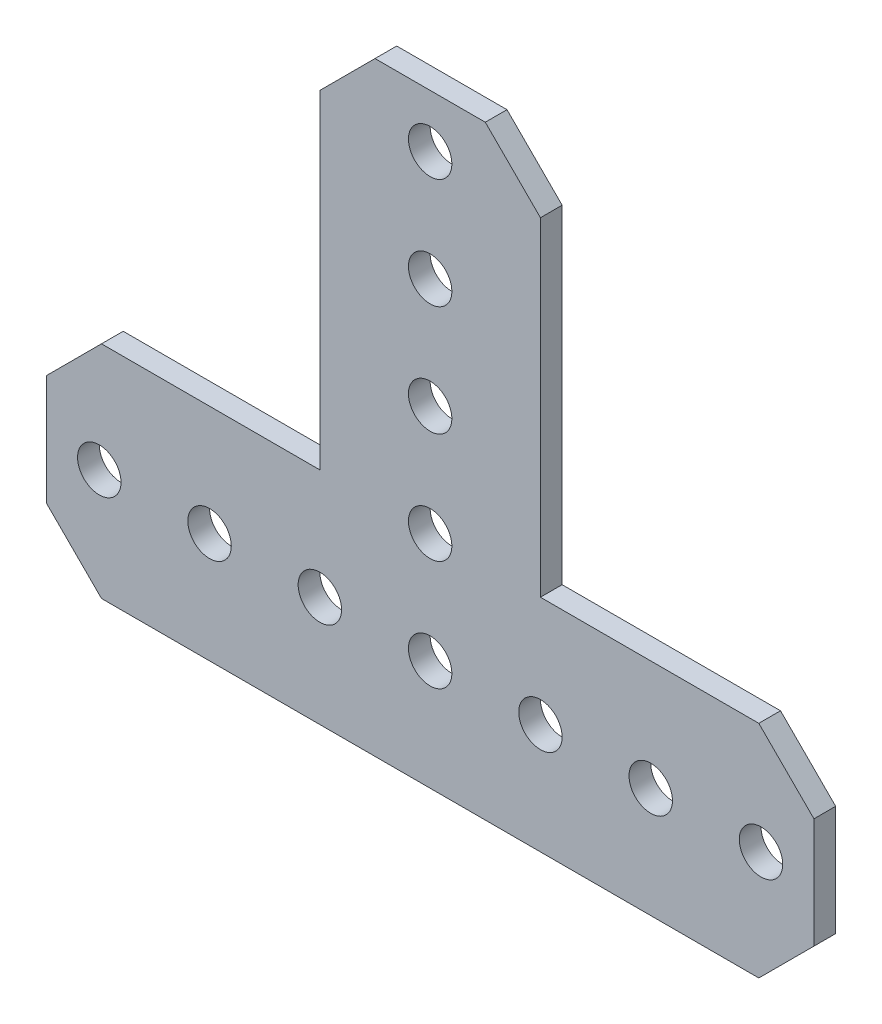
SolidWorks part; units mm, degrees
material "5052-H32"
ref_plane "Front Plane" through (0, 0, 0) normal (0, 0, 1) x (1, 0, 0)
ref_plane "Top Plane" through (0, 0, 0) normal (0, 1, 0) x (1, 0, 0)
ref_plane "Right Plane" through (0, 0, 0) normal (1, 0, 0) x (0, 0, -1)
ref_plane "Plane1" through (0, 0, -1.25) normal (0, 0, -1) x (-1, 0, 0)
sketch "Sketch1" plane through (0, 0, -1.25) normal (0, 0, -1) x (-1, 0, 0)
  line L0 (12.7, 12.7) -> (12.7, 50.546)
  line L1 (12.7, 50.546) -> (6.35, 56.896)
  line L2 (6.35, 56.896) -> (-6.35, 56.896)
  line L3 (-6.35, 56.896) -> (-12.7, 50.546)
  line L4 (-12.7, 50.546) -> (-12.7, 12.7)
  line L5 (-12.7, 12.7) -> (-37.846, 12.7)
  line L6 (-37.846, 12.7) -> (-44.196, 6.35)
  line L7 (-44.196, 6.35) -> (-44.196, -6.35)
  line L8 (-44.196, -6.35) -> (-37.846, -12.7)
  line L9 (-37.846, -12.7) -> (37.846, -12.7)
  line L10 (37.846, -12.7) -> (44.196, -6.35)
  line L11 (44.196, -6.35) -> (44.196, 6.35)
  line L12 (44.196, 6.35) -> (37.846, 12.7)
  line L13 (37.846, 12.7) -> (12.7, 12.7)
  circle A0 centre (0, 50.8) radius 2.5
  circle A1 centre (0, 38.1) radius 2.5
  circle A2 centre (-38.1, 0) radius 2.5
  circle A3 centre (-25.4, 0) radius 2.5
  circle A4 centre (-12.7, 0) radius 2.5
  circle A5 centre (0, 0) radius 2.5
  circle A6 centre (12.7, 0) radius 2.5
  circle A7 centre (38.1, 0) radius 2.5
  circle A8 centre (25.4, 0) radius 2.5
  circle A9 centre (0, 12.7) radius 2.5
  circle A10 centre (0, 25.4) radius 2.5
  point P36 (0, 0)
  dimension "D1" = 5
  dimension "D2" = 5
  dimension "D3" = 5
  dimension "D4" = 5
  dimension "D5" = 5
  dimension "D6" = 5
  dimension "D7" = 5
  dimension "D8" = 5
  dimension "D9" = 5
  dimension "D10" = 5
  dimension "D11" = 5
  dimension "D12" = 6.096
  dimension "D13" = 6.35
  dimension "D14" = 18.796
  dimension "D15" = 31.496
  dimension "D16" = 37.846
  dimension "D17" = 44.196
  dimension "D18" = 50.546
  dimension "D19" = 56.896
  dimension "D20" = 69.596
  dimension "D21" = 82.042
  dimension "D22" = 82.296
  dimension "D23" = 88.392
  dimension "D24" = 6.096
  dimension "D25" = 6.35
  dimension "D26" = 18.796
  dimension "D27" = 31.496
  dimension "D28" = 44.196
  dimension "D29" = 50.546
  dimension "D30" = 56.896
  dimension "D31" = 63.246
  dimension "D32" = 69.596
extrude "Boss-Extrude1" add sketch "Sketch1" against normal blind 2.5
